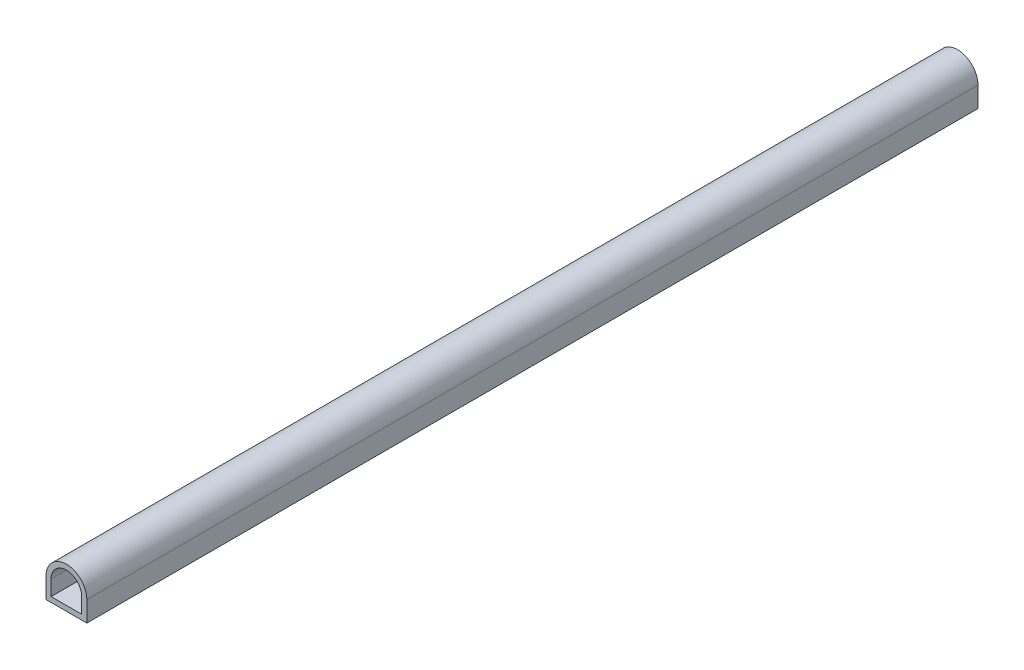
SolidWorks part; units mm, degrees
ref_plane "Plan de face" through (0, 0, 0) normal (0, 0, 1) x (1, 0, 0)
ref_plane "Plan de dessus" through (0, 0, 0) normal (0, 1, 0) x (1, 0, 0)
ref_plane "Plan de droite" through (0, 0, 0) normal (1, 0, 0) x (0, 0, -1)
sketch "Esquisse1" plane through (0, 0, 0) normal (0, 0, 1) x (1, 0, 0)
  line L0 (-2.25, -2.25) -> (2.25, -2.25)
  line L1 (-3, -3) -> (3, -3)
  line L2 (-3, -3) -> (-3, 0)
  line L3 (2.25, -2.25) -> (2.25, 0)
  line L4 (3, -3) -> (3, 0)
  line L5 (-2.25, -2.25) -> (-2.25, 0)
  arc A0 (3, 0) -> (-3, 0) centre (0, 0) ccw
  arc A1 (2.25, 0) -> (-2.25, 0) centre (0, 0) ccw
  dimension "D1" = 3
  dimension "D2" = 3
  dimension "D3" = 0.75
extrude "Extrusion1" add sketch "Esquisse1" along normal blind 131
